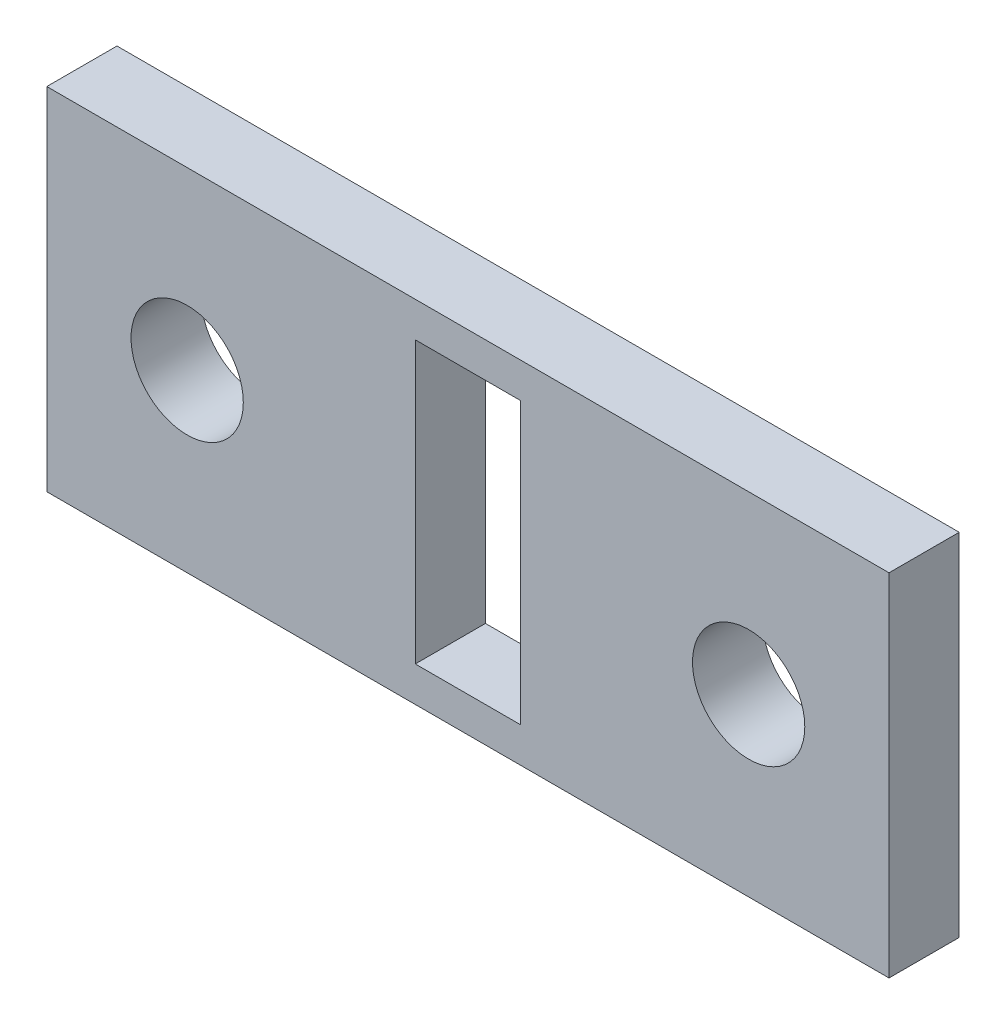
SolidWorks part; units mm, degrees
ref_plane "Front Plane" through (0, 0, 0) normal (0, 0, 1) x (1, 0, 0)
ref_plane "Top Plane" through (0, 0, 0) normal (0, 1, 0) x (1, 0, 0)
ref_plane "Right Plane" through (0, 0, 0) normal (1, 0, 0) x (0, 0, -1)
sketch "Sketch1" plane through (0, 0, 0) normal (0, 0, 1) x (1, 0, 0)
  line L1 (0, 0) -> (24, 0)
  line L2 (0, 0) -> (0, 10)
  line L3 (0, 10) -> (24, 10)
  line L4 (24, 0) -> (24, 10)
  dimension "D1" = 24
  dimension "D2" = 10
extrude "Boss-Extrude1" add sketch "Sketch1" along normal blind 2
sketch "Sketch2" plane through (0, 0, 2) normal (0, 0, 1) x (1, 0, 0)
  line L0 (0, 5) -> (24, 5) construction
  line L1 (0, 10) -> (0, 0) construction
  line L2 (24, 0) -> (24, 10) construction
  line L3 (4, 5) -> (20, 5) construction
  circle A0 centre (4, 5) radius 1.6
  circle A1 centre (20, 5) radius 1.6
  point P10 (12, 5)
  point P11 (12, 5)
  dimension "D1" = 16
  dimension "D2" = 3.2
  dimension "D3" = 3.2
extrude "Cut-Extrude1" cut sketch "Sketch2" against normal blind 2
sketch "Sketch3" plane through (0, 0, 2) normal (0, 0, 1) x (1, 0, 0)
  line L0 (4, 5) -> (20, 5) construction
  line L1 (13.5, 9) -> (10.5, 1) construction
  line L2 (10.5, 9) -> (13.5, 9)
  line L3 (10.5, 9) -> (10.5, 1)
  line L4 (10.5, 1) -> (13.5, 1)
  line L5 (13.5, 9) -> (13.5, 1)
  point P8 (12, 5)
  point P9 (12, 5)
  dimension "D1" = 3
  dimension "D2" = 8
extrude "Cut-Extrude2" cut sketch "Sketch3" against normal blind 2
